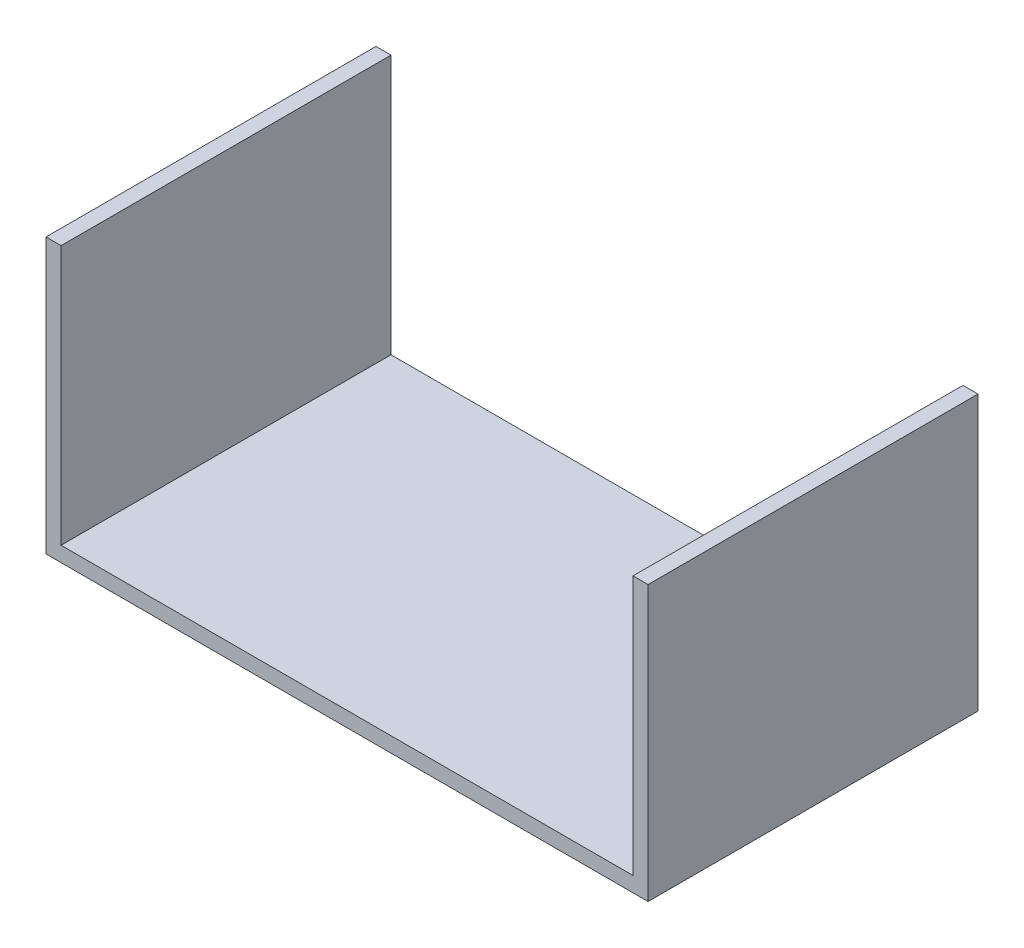
SolidWorks part; units mm, degrees
material "6061-T6 (SS)"
ref_plane "Front Plane" through (0, 0, 0) normal (0, 0, 1) x (1, 0, 0)
ref_plane "Top Plane" through (0, 0, 0) normal (0, 1, 0) x (1, 0, 0)
ref_plane "Right Plane" through (0, 0, 0) normal (1, 0, 0) x (0, 0, -1)
sketch "Sketch1" plane through (0, 0, 0) normal (0, 0, 1) x (1, 0, 0)
  line L0 (-3.175, -3.175) -> (-3.175, 54.737)
  line L1 (0, 0) -> (120.65, 0)
  line L2 (0, 0) -> (0, 51.562)
  line L3 (0, 51.562) -> (0, 54.737)
  line L4 (123.825, 54.737) -> (120.65, 54.737)
  line L5 (-3.175, 54.737) -> (0, 54.737)
  line L6 (123.825, -3.175) -> (123.825, 54.737)
  line L7 (-3.175, -3.175) -> (123.825, -3.175)
  line L8 (0, 51.562) -> (120.65, 51.562) construction
  line L9 (120.65, 54.737) -> (120.65, 0)
  line L11 (-3.175, 54.737) -> (123.825, 54.737) construction
  line L12 (120.65, 0) -> (120.65, 51.562) construction
  dimension "D2" = 127
  dimension "D3" = 57.912
  dimension "D4" = 57.912
  dimension "D5" = 3.175
  dimension "D1" = 3.175
extrude "Boss-Extrude1" add sketch "Sketch1" along normal blind 69.596
